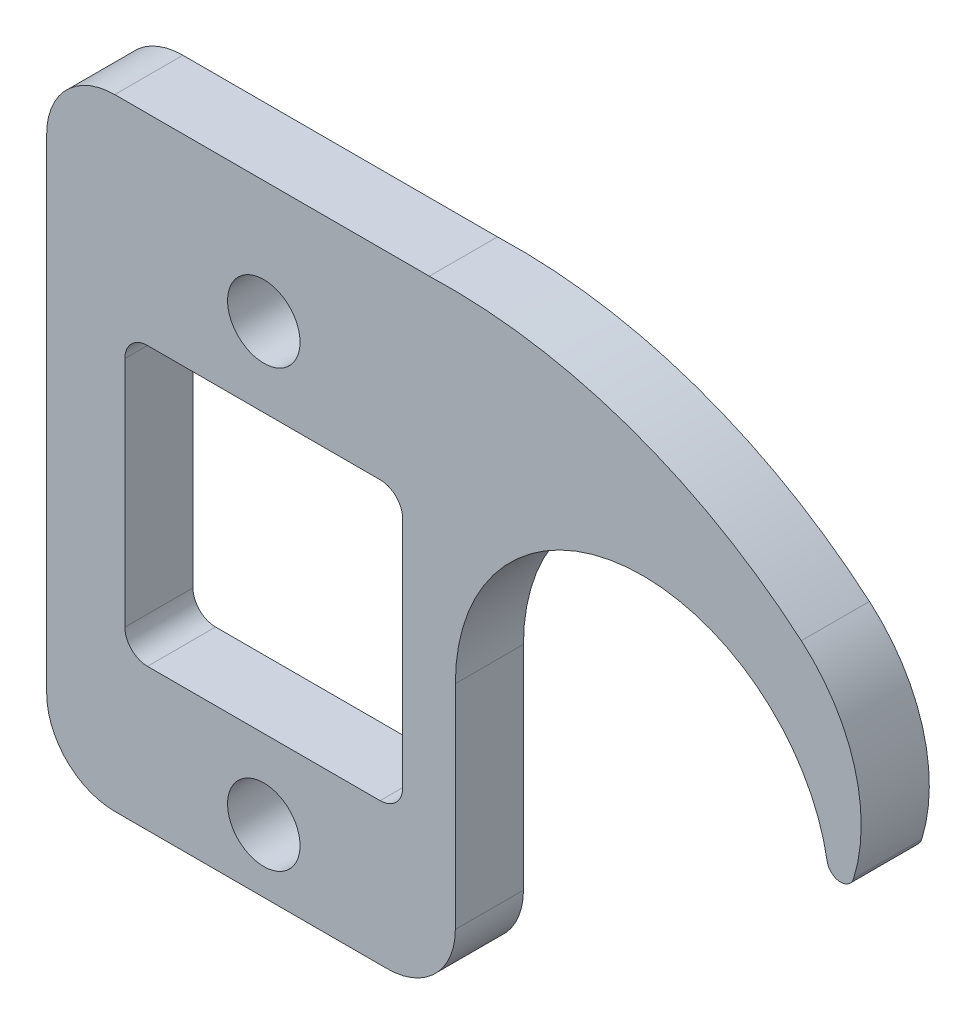
SolidWorks part; units mm, degrees
ref_plane "Front Plane" through (0, 0, 0) normal (0, 0, 1) x (1, 0, 0)
ref_plane "Top Plane" through (0, 0, 0) normal (0, 1, 0) x (1, 0, 0)
ref_plane "Right Plane" through (0, 0, 0) normal (1, 0, 0) x (0, 0, -1)
sketch "Sketch1" plane through (0, 0, 0) normal (0, 0, 1) x (1, 0, 0)
  line L0 (-19.8857, 31.6857) -> (-49.2125, 31.6857)
  line L1 (-55.5625, 25.3357) -> (-55.5625, -19.8437)
  line L2 (-49.2125, -26.1938) -> (-23.8125, -26.1938)
  line L3 (-17.4625, -19.8437) -> (-17.4625, 0)
  line L4 (-48.2759, 10.8458) -> (-48.2759, -10.8458)
  line L5 (-46.1677, -12.954) -> (-24.4761, -12.954)
  line L6 (-22.3679, -10.8458) -> (-22.3679, 10.8458)
  line L7 (-24.4761, 12.954) -> (-46.1677, 12.954)
  circle A0 centre (-35.3219, -20.32) radius 3.3782
  arc A1 (-49.2125, 31.6857) -> (-55.5625, 25.3357) centre (-49.2125, 25.3357) ccw
  arc A2 (-55.5625, -19.8437) -> (-49.2125, -26.1938) centre (-49.2125, -19.8438) ccw
  arc A3 (-23.8125, -26.1938) -> (-17.4625, -19.8437) centre (-23.8125, -19.8438) ccw
  arc A4 (17.2058, 2.9834) -> (-17.4625, 0) centre (0, 0) ccw
  arc A5 (17.2058, 2.9834) -> (19.6706, 2.8257) centre (18.4571, 3.2003) ccw
  arc A6 (19.6706, 2.8257) -> (14.7931, 19.5955) centre (4.5018, 7.5081) ccw
  arc A7 (14.7931, 19.5955) -> (-19.8857, 31.6857) centre (-18.1389, -19.0842) ccw
  circle A8 centre (-35.3219, 20.32) radius 3.3782
  arc A9 (-46.1677, 12.954) -> (-48.2759, 10.8458) centre (-46.1677, 10.8458) ccw
  arc A10 (-48.2759, -10.8458) -> (-46.1677, -12.954) centre (-46.1677, -10.8458) ccw
  arc A11 (-24.4761, -12.954) -> (-22.3679, -10.8458) centre (-24.4761, -10.8458) ccw
  arc A12 (-22.3679, 10.8458) -> (-24.4761, 12.954) centre (-24.4761, 10.8458) ccw
  point P13 (0, 0)
  dimension "D1" = 6.7564
  dimension "D2" = 6.35
  dimension "D3" = 17.4625
  dimension "D4" = 1.27
  dimension "D5" = 15.875
  dimension "D6" = 50.8
  dimension "D7" = 2.1082
  dimension "D8" = 4.5018
  dimension "D9" = 14.7931
  dimension "D10" = 17.2058
  dimension "D11" = 19.8857
  dimension "D12" = 22.3679
  dimension "D13" = 35.3219
  dimension "D14" = 48.2759
  dimension "D15" = 55.5625
  dimension "D16" = 12.954
  dimension "D17" = 20.32
  dimension "D19" = 20.32
  dimension "D20" = 26.1938
extrude "Boss-Extrude1" add sketch "Sketch1" along normal mid plane 6.35
